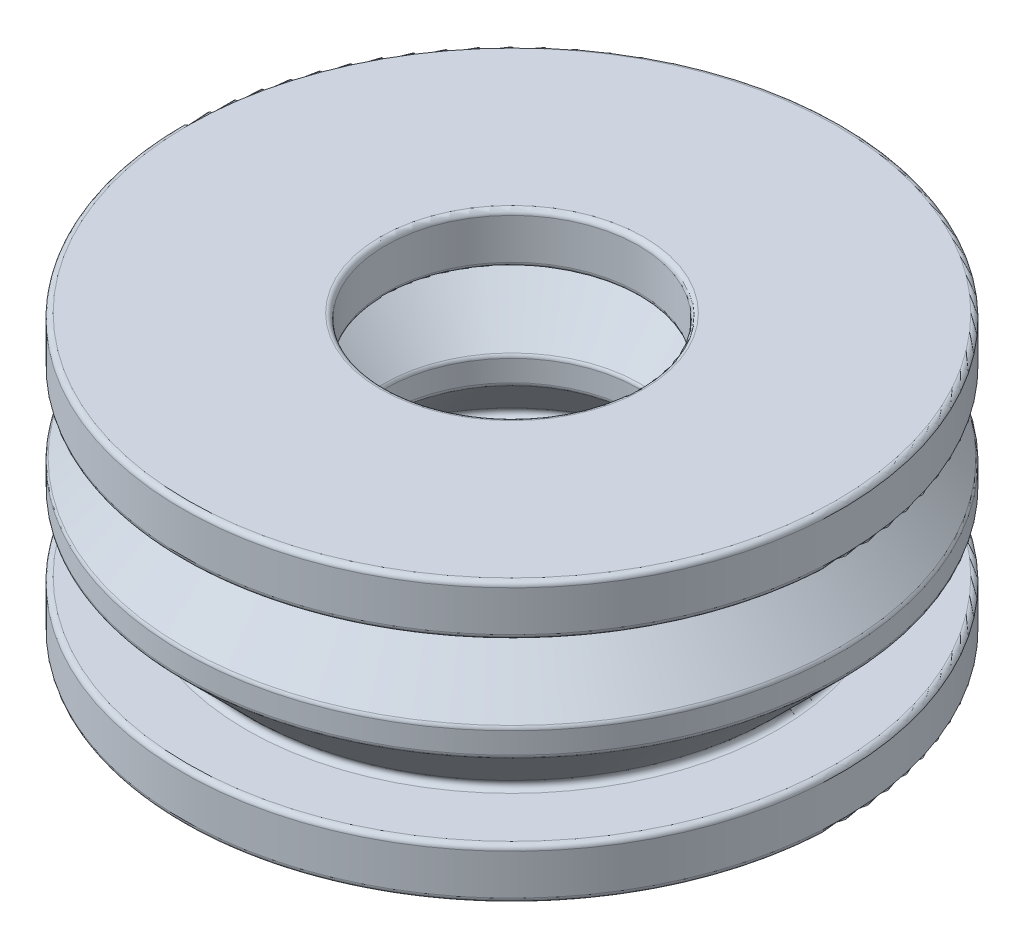
SolidWorks part; units mm, degrees
material "AISI 304"
ref_plane "前视基准面" through (0, 0, 0) normal (0, 0, 1) x (1, 0, 0)
ref_plane "上视基准面" through (0, 0, 0) normal (0, 1, 0) x (1, 0, 0)
ref_plane "右视基准面" through (0, 0, 0) normal (1, 0, 0) x (0, 0, -1)
sketch "草图1" plane through (0, 0, 0) normal (0, 0, 1) x (1, 0, 0)
  line L0 (0, 0) -> (0, 5) construction
  line L1 (-5, 0.2) -> (-5, 1.8)
  line L2 (-5.2, 11) -> (-12.8, 11)
  line L3 (-13, 10.8) -> (-13, 9.2)
  line L4 (-12.8, 0) -> (-5.2, 0)
  line L5 (-12.8, 9) -> (-10.4828, 9)
  line L6 (-10.3414, 8.6586) -> (-12.9414, 6.0586)
  line L7 (-12.9414, 4.9414) -> (-10.3414, 2.3414)
  line L8 (-10.4828, 2) -> (-12.8, 2)
  line L9 (-5.2, 9) -> (-7.5172, 9)
  line L10 (-7.6586, 8.6586) -> (-5.0586, 6.0586)
  line L11 (-5.2, 2) -> (-7.5172, 2)
  line L12 (-7.6586, 2.3414) -> (-5.0586, 4.9414)
  line L13 (-13, 5.9172) -> (-13, 5.0828)
  line L14 (-13, 1.8) -> (-13, 0.2)
  line L15 (-5, 9.2) -> (-5, 10.8)
  line L16 (-5, 5.0828) -> (-5, 5.9172)
  arc A0 (-5.0586, 4.9414) -> (-5, 5.0828) centre (-5.2, 5.0828) ccw
  arc A1 (-7.5172, 2) -> (-7.6586, 2.3414) centre (-7.5172, 2.2) cw
  arc A2 (-5.2, 2) -> (-5, 1.8) centre (-5.2, 1.8) cw
  arc A3 (-5.0586, 6.0586) -> (-5, 5.9172) centre (-5.2, 5.9172) cw
  arc A4 (-7.5172, 9) -> (-7.6586, 8.6586) centre (-7.5172, 8.8) ccw
  arc A5 (-12.8, 2) -> (-13, 1.8) centre (-12.8, 1.8) ccw
  arc A6 (-5.2, 9) -> (-5, 9.2) centre (-5.2, 9.2) ccw
  arc A7 (-10.3414, 2.3414) -> (-10.4828, 2) centre (-10.4828, 2.2) cw
  arc A8 (-12.9414, 6.0586) -> (-13, 5.9172) centre (-12.8, 5.9172) ccw
  arc A9 (-12.9414, 4.9414) -> (-13, 5.0828) centre (-12.8, 5.0828) cw
  arc A10 (-10.4828, 9) -> (-10.3414, 8.6586) centre (-10.4828, 8.8) cw
  arc A11 (-13, 0.2) -> (-12.8, 0) centre (-12.8, 0.2) ccw
  arc A12 (-12.8, 9) -> (-13, 9.2) centre (-12.8, 9.2) cw
  arc A13 (-12.8, 11) -> (-13, 10.8) centre (-12.8, 10.8) ccw
  arc A14 (-5, 10.8) -> (-5.2, 11) centre (-5.2, 10.8) ccw
  arc A15 (-5, 0.2) -> (-5.2, 0) centre (-5.2, 0.2) cw
  point P22 (-5, 5)
  point P33 (-13, 2)
  point P36 (-5, 9)
  point P39 (-10, 2)
  point P42 (-13, 6)
  point P45 (-13, 5)
  point P48 (-10, 9)
  point P51 (-13, 0)
  point P54 (-13, 9)
  point P57 (-13, 11)
  dimension "D8" = 0.2
  dimension "D1" = 11
  dimension "D2" = 10
  dimension "D3" = 26
  dimension "D4" = 2
  dimension "D5" = 2
  dimension "D6" = 3
  dimension "D7" = 45
revolve "旋转1" add sketch "草图1" angle 360 about L0
